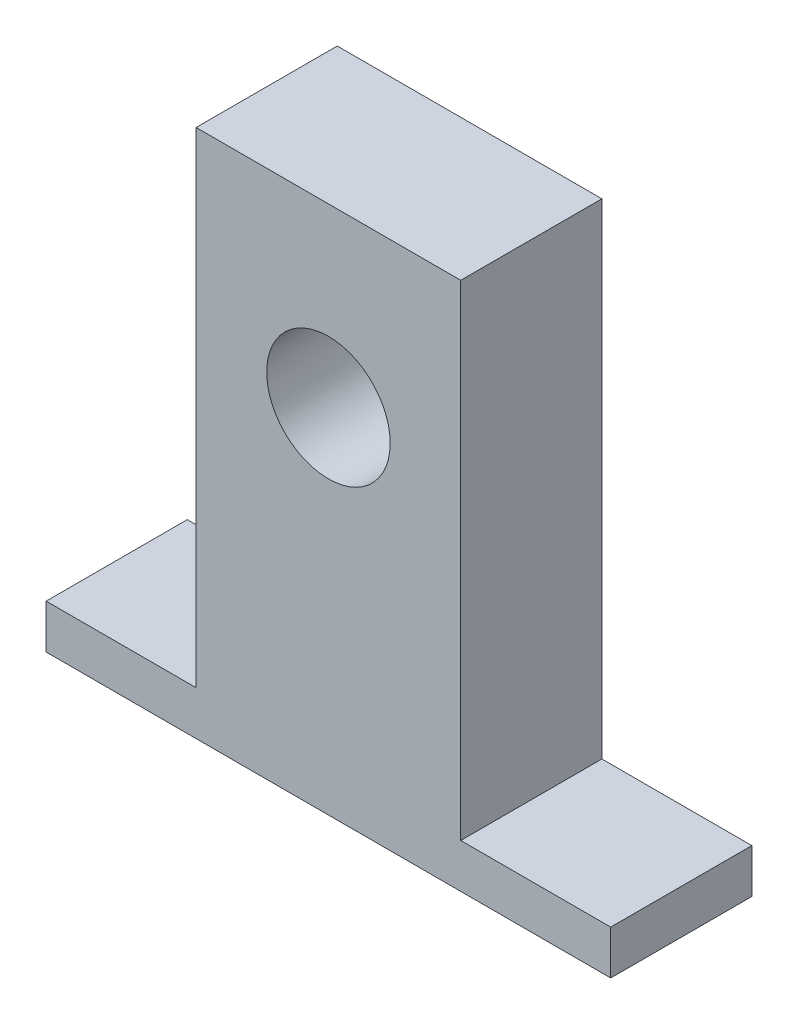
SolidWorks part; units mm, degrees
ref_plane "Front Plane" through (0, 0, 0) normal (0, 0, 1) x (1, 0, 0)
ref_plane "Top Plane" through (0, 0, 0) normal (0, 1, 0) x (1, 0, 0)
ref_plane "Right Plane" through (0, 0, 0) normal (1, 0, 0) x (0, 0, -1)
sketch "Sketch1" plane through (0, 0, 0) normal (0, 1, 0) x (1, 0, 0)
  line L1 (-32, -8) -> (32, -8)
  line L2 (-32, -8) -> (-32, 8)
  line L3 (-32, 8) -> (32, 8)
  line L4 (32, -8) -> (32, 8)
  line L5 (-32, -8) -> (32, 8) construction
  line L6 (-32, 8) -> (32, -8) construction
  point P0 (0, 0)
  dimension "D1" = 64
  dimension "D2" = 16
extrude "Boss-Extrude1" add sketch "Sketch1" along normal blind 5
sketch "Sketch2" plane through (0, 5, 0) normal (0, 1, 0) x (1, 0, 0)
  line L0 (32, 8) -> (-32, 8) construction
  line L1 (-15, -8) -> (15, -8)
  line L2 (-15, -8) -> (-15, 8)
  line L3 (-15, 8) -> (15, 8)
  line L4 (15, -8) -> (15, 8)
  line L5 (-15, -8) -> (15, 8) construction
  line L6 (-15, 8) -> (15, -8) construction
  point P0 (0, 0)
  dimension "D1" = 30
extrude "Boss-Extrude2" add sketch "Sketch2" along normal blind 55
sketch "Sketch3" plane through (0, 0, 8) normal (0, 0, 1) x (1, 0, 0)
  line L0 (-15, 60) -> (15, 60) construction
  circle A0 centre (0, 40) radius 7
  dimension "D2" = 14
  dimension "D1" = 20
extrude "Cut-Extrude1" cut sketch "Sketch3" against normal blind 55
